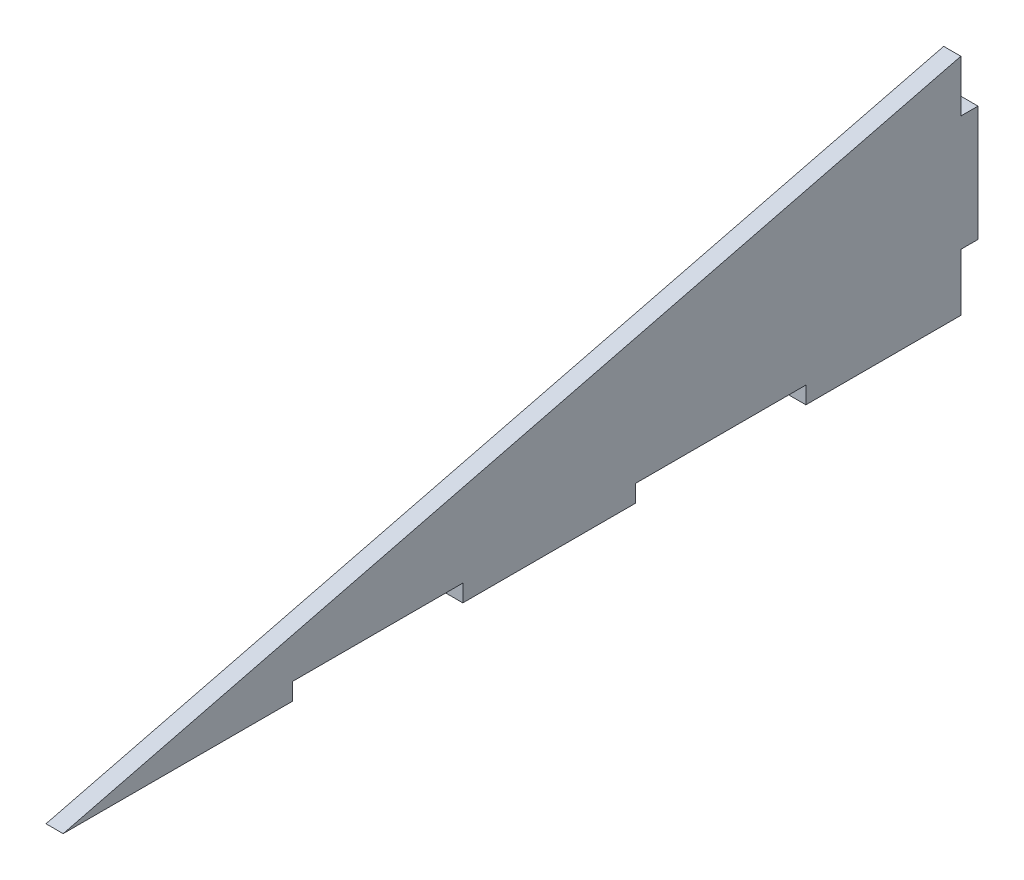
SolidWorks part; units mm, degrees
ref_plane "Front Plane" through (0, 0, 0) normal (0, 0, 1) x (1, 0, 0)
ref_plane "Top Plane" through (0, 0, 0) normal (0, 1, 0) x (1, 0, 0)
ref_plane "Right Plane" through (0, 0, 0) normal (1, 0, 0) x (0, 0, -1)
sketch "Sketch2" plane through (0, 0, 0) normal (1, 0, 0) x (0, 0, -1)
  line L0 (0, 0) -> (160, 40)
  line L1 (0, 0) -> (160, 0)
  line L2 (0, 0) -> (0, 40)
  line L3 (0, 40) -> (160, 40)
  line L4 (160, 0) -> (160, 40)
  line L5 (157, 30.2) -> (157, 39.25)
  line L6 (160, 30.2) -> (157, 30.2)
  line L7 (160, 30.2) -> (160, 10)
  line L8 (160, 10) -> (157, 10)
  line L10 (100.1, 0) -> (100.1, 3)
  line L11 (40.1, 0) -> (69.9, 0)
  line L12 (157, 10) -> (157, 0)
  line L13 (40.1, 0) -> (40.1, 3)
  line L14 (40.1, 3) -> (69.9, 3)
  line L15 (69.9, 0) -> (69.9, 3)
  line L16 (100.1, 0) -> (129.9, 0)
  line L17 (129.9, 0) -> (129.9, 3)
  line L18 (100.1, 3) -> (129.9, 3)
  dimension "D1" = 160
  dimension "D2" = 40
  dimension "D3" = 20.2
  dimension "D4" = 10
  dimension "D5" = 3
  dimension "D6" = 3
  dimension "D7" = 3
  dimension "D8" = 40.1
  dimension "D9" = 29.8
  dimension "D11" = 30.2
  dimension "D10" = 2
extrude "Boss-Extrude1" add sketch "Sketch2" along normal blind 3 contours L10 L18 L17 L1 L12 L8 L4 L6 L5 L0 L13 L14 L15
